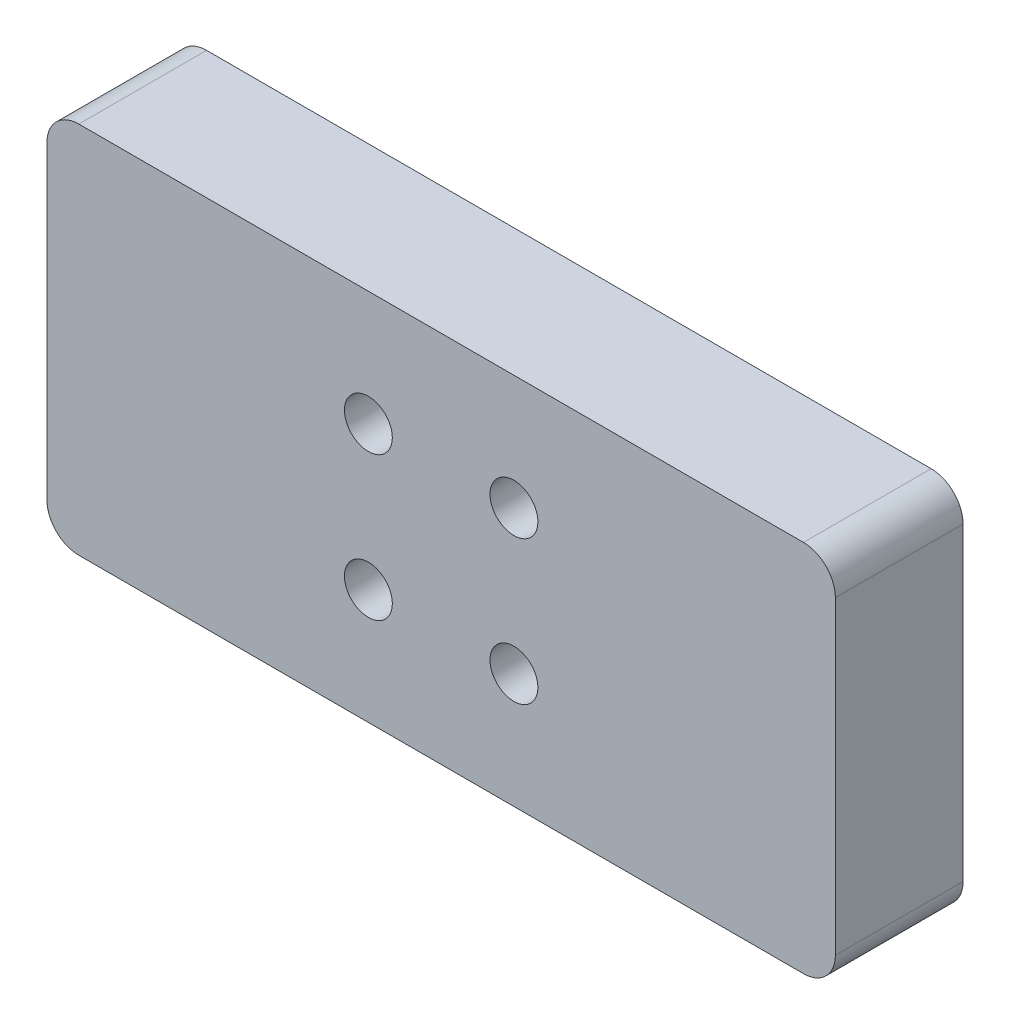
SolidWorks part; units mm, degrees
ref_plane "Front Plane" through (0, 0, 0) normal (0, 0, 1) x (1, 0, 0)
ref_plane "Top Plane" through (0, 0, 0) normal (0, 1, 0) x (1, 0, 0)
ref_plane "Right Plane" through (0, 0, 0) normal (1, 0, 0) x (0, 0, -1)
sketch "Sketch1" plane through (0, 0, 0) normal (0, 0, 1) x (1, 0, 0)
  line L1 (-31.369, -14.859) -> (31.369, -14.859)
  line L2 (-31.369, -14.859) -> (-31.369, 14.859)
  line L3 (-31.369, 14.859) -> (31.369, 14.859)
  line L4 (31.369, -14.859) -> (31.369, 14.859)
  line L5 (-31.369, -14.859) -> (31.369, 14.859) construction
  line L6 (-31.369, 14.859) -> (31.369, -14.859) construction
  point P0 (0, 0)
  dimension "D1" = 29.718
  dimension "D2" = 62.738
extrude "Boss-Extrude1" add sketch "Sketch1" along normal mid plane 10.16
fillet "Fillet1" radius 2.54 4 edges at (31.369, 14.859, 0) (31.369, -14.859, 0) (-31.369, -14.859, 0) (-31.369, 14.859, 0)
sketch "Sketch2" plane through (0, 0, 5.08) normal (0, 0, 1) x (1, 0, 0)
  line L1 (-5.7912, -5.715) -> (5.7912, -5.715) construction
  line L2 (-5.7912, -5.715) -> (-5.7912, 5.715) construction
  line L3 (-5.7912, 5.715) -> (5.7912, 5.715) construction
  line L4 (5.7912, -5.715) -> (5.7912, 5.715) construction
  line L5 (-5.7912, -5.715) -> (5.7912, 5.715) construction
  line L6 (-5.7912, 5.715) -> (5.7912, -5.715) construction
  circle A0 centre (-5.7912, 5.715) radius 1.905
  circle A1 centre (5.7912, 5.715) radius 1.905
  circle A2 centre (5.7912, -5.715) radius 1.905
  circle A3 centre (-5.7912, -5.715) radius 1.905
  point P0 (0, 0)
  dimension "D3" = 3.81
  dimension "D4" = 3.81
  dimension "D5" = 3.81
  dimension "D6" = 3.81
  dimension "D1" = 11.43
  dimension "D2" = 11.5824
extrude "Cut-Extrude1" cut sketch "Sketch2" against normal mid plane 10
sketch "Sketch3" plane through (0, 0, -5.08) normal (0, 0, -1) x (-1, 0, 0)
  line L1 (-25.4, -7.9375) -> (25.4, -7.9375) construction
  line L2 (-25.4, -7.9375) -> (-25.4, 7.9375) construction
  line L3 (-25.4, 7.9375) -> (25.4, 7.9375) construction
  line L4 (25.4, -7.9375) -> (25.4, 7.9375) construction
  line L5 (-25.4, -7.9375) -> (25.4, 7.9375) construction
  line L6 (-25.4, 7.9375) -> (25.4, -7.9375) construction
  circle A0 centre (-25.4, 7.9375) radius 1.905
  circle A1 centre (-25.4, -7.9375) radius 1.905
  circle A2 centre (25.4, -7.9375) radius 1.905
  circle A3 centre (25.4, 7.9375) radius 1.905
  point P0 (0, 0)
  dimension "D3" = 3.81
  dimension "D4" = 3.81
  dimension "D5" = 3.81
  dimension "D6" = 3.81
  dimension "D1" = 15.875
  dimension "D2" = 50.8
extrude "Cut-Extrude2" cut sketch "Sketch3" against normal mid plane 6
